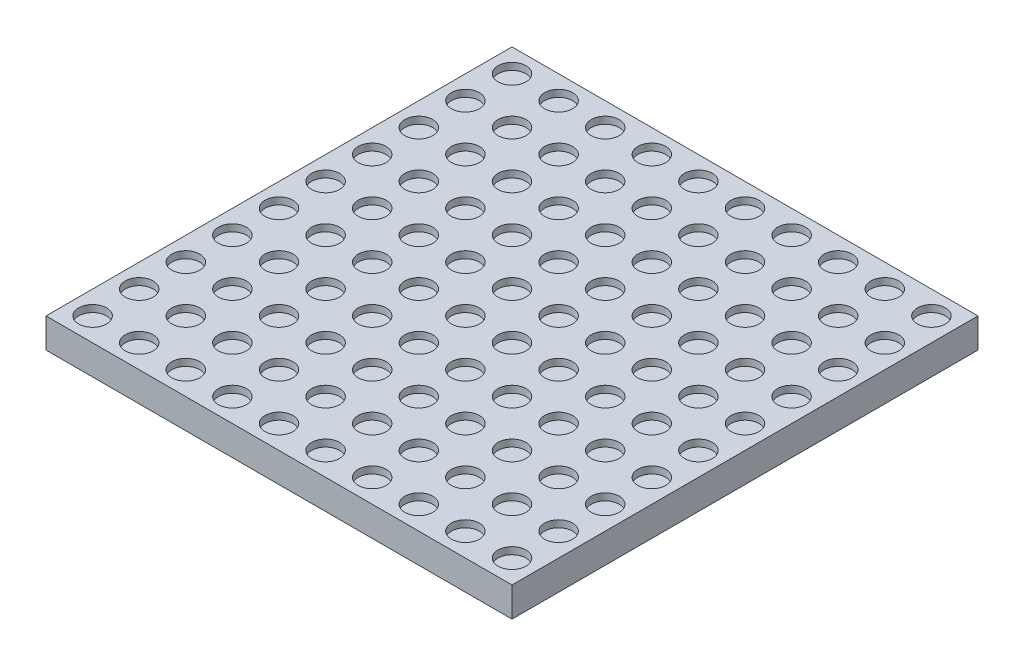
SolidWorks part; units mm, degrees
ref_plane "Front Plane" through (0, 0, 0) normal (0, 0, 1) x (1, 0, 0)
ref_plane "Top Plane" through (0, 0, 0) normal (0, 1, 0) x (1, 0, 0)
ref_plane "Right Plane" through (0, 0, 0) normal (1, 0, 0) x (0, 0, -1)
sketch "Sketch1" plane through (0, 0, 0) normal (0, 1, 0) x (1, 0, 0)
  line L1 (0, 0) -> (100, 0)
  line L2 (0, 0) -> (0, 100)
  line L3 (0, 100) -> (100, 100)
  line L4 (100, 0) -> (100, 100)
  dimension "D1" = 100
  dimension "D2" = 100
extrude "Boss-Extrude1" add sketch "Sketch1" along normal blind 6.35
sketch "Sketch2" plane through (0, 6.35, 0) normal (0, 1, 0) x (1, 0, 0)
  line L1 (100, 100) -> (0, 100) construction
  line L2 (0, 100) -> (0, 0) construction
  circle A0 centre (5, 95) radius 3
  circle A1 centre (15, 95) radius 3
  circle A2 centre (25, 95) radius 3
  circle A3 centre (35, 95) radius 3
  circle A4 centre (45, 95) radius 3
  circle A5 centre (55, 95) radius 3
  circle A6 centre (65, 95) radius 3
  circle A7 centre (75, 95) radius 3
  circle A8 centre (85, 95) radius 3
  circle A9 centre (95, 95) radius 3
  circle A10 centre (15, 85) radius 3
  circle A11 centre (25, 85) radius 3
  circle A12 centre (35, 85) radius 3
  circle A13 centre (45, 85) radius 3
  circle A14 centre (55, 85) radius 3
  circle A15 centre (65, 85) radius 3
  circle A16 centre (75, 85) radius 3
  circle A17 centre (85, 85) radius 3
  circle A18 centre (95, 85) radius 3
  circle A19 centre (15, 75) radius 3
  circle A20 centre (25, 75) radius 3
  circle A21 centre (35, 75) radius 3
  circle A22 centre (45, 75) radius 3
  circle A23 centre (55, 75) radius 3
  circle A24 centre (65, 75) radius 3
  circle A25 centre (75, 75) radius 3
  circle A26 centre (85, 75) radius 3
  circle A27 centre (95, 75) radius 3
  circle A28 centre (15, 65) radius 3
  circle A29 centre (25, 65) radius 3
  circle A30 centre (35, 65) radius 3
  circle A31 centre (45, 65) radius 3
  circle A32 centre (55, 65) radius 3
  circle A33 centre (65, 65) radius 3
  circle A34 centre (75, 65) radius 3
  circle A35 centre (85, 65) radius 3
  circle A36 centre (95, 65) radius 3
  circle A37 centre (15, 55) radius 3
  circle A38 centre (25, 55) radius 3
  circle A39 centre (35, 55) radius 3
  circle A40 centre (45, 55) radius 3
  circle A41 centre (55, 55) radius 3
  circle A42 centre (65, 55) radius 3
  circle A43 centre (75, 55) radius 3
  circle A44 centre (85, 55) radius 3
  circle A45 centre (95, 55) radius 3
  circle A46 centre (15, 45) radius 3
  circle A47 centre (25, 45) radius 3
  circle A48 centre (35, 45) radius 3
  circle A49 centre (45, 45) radius 3
  circle A50 centre (55, 45) radius 3
  circle A51 centre (65, 45) radius 3
  circle A52 centre (75, 45) radius 3
  circle A53 centre (85, 45) radius 3
  circle A54 centre (95, 45) radius 3
  circle A55 centre (15, 35) radius 3
  circle A56 centre (25, 35) radius 3
  circle A57 centre (35, 35) radius 3
  circle A58 centre (45, 35) radius 3
  circle A59 centre (55, 35) radius 3
  circle A60 centre (65, 35) radius 3
  circle A61 centre (75, 35) radius 3
  circle A62 centre (85, 35) radius 3
  circle A63 centre (95, 35) radius 3
  circle A64 centre (15, 25) radius 3
  circle A65 centre (25, 25) radius 3
  circle A66 centre (35, 25) radius 3
  circle A67 centre (45, 25) radius 3
  circle A68 centre (55, 25) radius 3
  circle A69 centre (65, 25) radius 3
  circle A70 centre (75, 25) radius 3
  circle A71 centre (85, 25) radius 3
  circle A72 centre (95, 25) radius 3
  circle A73 centre (15, 15) radius 3
  circle A74 centre (25, 15) radius 3
  circle A75 centre (35, 15) radius 3
  circle A76 centre (45, 15) radius 3
  circle A77 centre (55, 15) radius 3
  circle A78 centre (65, 15) radius 3
  circle A79 centre (75, 15) radius 3
  circle A80 centre (85, 15) radius 3
  circle A81 centre (95, 15) radius 3
  circle A82 centre (15, 5) radius 3
  circle A83 centre (25, 5) radius 3
  circle A84 centre (35, 5) radius 3
  circle A85 centre (45, 5) radius 3
  circle A86 centre (55, 5) radius 3
  circle A87 centre (65, 5) radius 3
  circle A88 centre (75, 5) radius 3
  circle A89 centre (85, 5) radius 3
  circle A90 centre (95, 5) radius 3
  circle A91 centre (5, 85) radius 3
  circle A92 centre (5, 75) radius 3
  circle A93 centre (5, 65) radius 3
  circle A94 centre (5, 55) radius 3
  circle A95 centre (5, 45) radius 3
  circle A96 centre (5, 35) radius 3
  circle A97 centre (5, 25) radius 3
  circle A98 centre (5, 15) radius 3
  circle A99 centre (5, 5) radius 3
  dimension "D1" = 6
  dimension "D4" = 5
  dimension "D5" = 5
  dimension "D2" = 10
  dimension "D3" = 10
extrude "Cut-Extrude1" cut sketch "Sketch2" against normal blind 1.5
